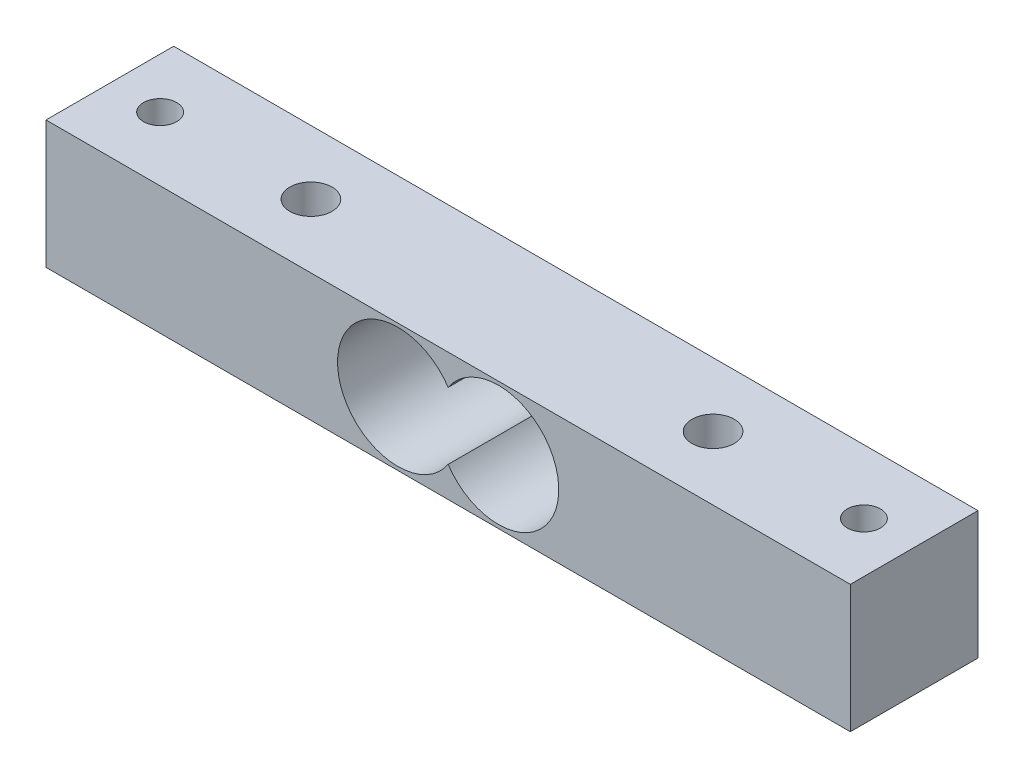
SolidWorks part; units mm, degrees
ref_plane "Front Plane" through (0, 0, 0) normal (0, 0, 1) x (1, 0, 0)
ref_plane "Top Plane" through (0, 0, 0) normal (0, 1, 0) x (1, 0, 0)
ref_plane "Right Plane" through (0, 0, 0) normal (1, 0, 0) x (0, 0, -1)
sketch "Sketch1" plane through (0, 0, 0) normal (0, 1, 0) x (1, 0, 0)
  line L1 (-40, -6.35) -> (40, -6.35)
  line L2 (-40, -6.35) -> (-40, 6.35)
  line L3 (-40, 6.35) -> (40, 6.35)
  line L4 (40, -6.35) -> (40, 6.35)
  line L5 (-40, -6.35) -> (40, 6.35) construction
  line L6 (-40, 6.35) -> (40, -6.35) construction
  point P0 (0, 0)
  dimension "D1" = 80
  dimension "D2" = 12.7
extrude "Boss-Extrude1" add sketch "Sketch1" along normal mid plane 12.7
sketch "Sketch2" plane through (0, 0, 6.35) normal (0, 0, 1) x (1, 0, 0)
  line L0 (-27.8204, 0) -> (32.7694, 0) construction
  circle A0 centre (-5, 0) radius 6
  circle A1 centre (5, 0) radius 6
  dimension "D3" = 12
  dimension "D1" = 5
  dimension "D2" = 5
extrude "Cut-Extrude1" cut sketch "Sketch2" against normal through all contours A0 L0 A1 | L0 A0 A1 | A0 L0 A1 | L0 A0 A1 | A1 L0 A0 | L0 A1 A0
hole_wizard "M4x0.7 Tapped Hole2" positions "Sketch3" profile "Sketch4" tap size "M4x0.7" standard "ANSI Metric" end condition up to next
sketch "Sketch3" plane through (0, 6.35, 0) normal (0, 1, 0) x (1, 0, 0)
  line L0 (-41.6939, 0) -> (44.7232, 0) construction
  line L2 (0, 0) -> (0, -29.5365) construction
  line L3 (40, -6.35) -> (40, 6.35) construction
  point P24 (35, 0)
  point P36 (-35, 0)
  dimension "D1" = 5
sketch "Sketch4" plane through (-35, 6.35, 0) normal (1, 0, 0) x (0, 0, 1)
  line L0 (0, 0) -> (0, 12.7)
  line L1 (0, 12.7) -> (1.65, 12.7)
  line L2 (1.65, 12.7) -> (1.65, 0)
  line L5 (1.65, 0) -> (0, 0)
  line L11 (0, -6.35) -> (0, 107.95) construction
  dimension "Thru Tap Drill Dia." = 3.3
  dimension "Thru Tap Drill Depth" = 12.7
cosmetic thread "Hole Thread5" parameters "D2"=4
cosmetic thread "Hole Thread6" parameters "D2"=4
hole_wizard "M5x0.8 Tapped Hole2" positions "Sketch5" profile "Sketch6" tap size "M5x0.8" standard "ANSI Metric" end condition up to next
sketch "Sketch5" plane through (0, 6.35, 0) normal (0, 1, 0) x (1, 0, 0)
  line L0 (40, -6.35) -> (40, 6.35) construction
  line L3 (0, 12.7978) -> (0, -9.1413) construction
  line L6 (-52.7219, 0) -> (46.5143, 0) construction
  point P2 (20, 0)
  point P25 (-20, 0)
  dimension "D1" = 20
sketch "Sketch6" plane through (20, 6.35, 0) normal (1, 0, 0) x (0, 0, 1)
  line L0 (0, 0) -> (0, 12.7)
  line L1 (0, 12.7) -> (2.1, 12.7)
  line L2 (2.1, 12.7) -> (2.1, 0)
  line L5 (2.1, 0) -> (0, 0)
  line L11 (0, -6.35) -> (0, 107.95) construction
  dimension "Thru Tap Drill Dia." = 4.2
  dimension "Thru Tap Drill Depth" = 12.7
cosmetic thread "Hole Thread7" parameters "D2"=5
cosmetic thread "Hole Thread8" parameters "D2"=5
